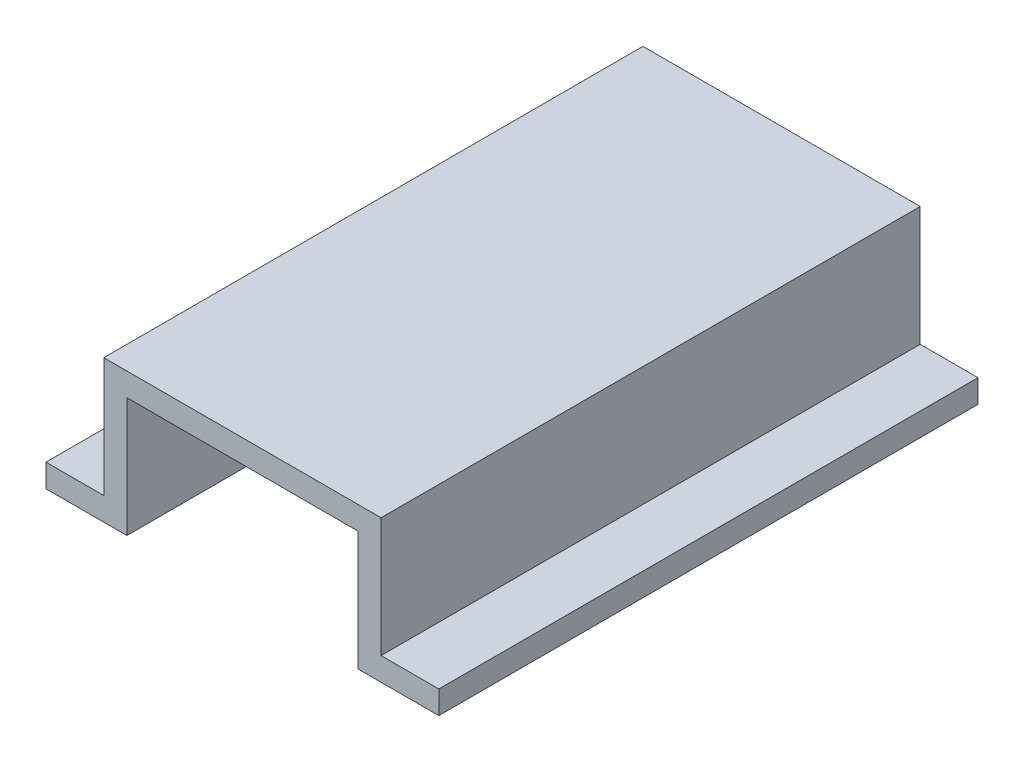
SolidWorks part; units mm, degrees
ref_plane "Front Plane" through (0, 0, 0) normal (0, 0, 1) x (1, 0, 0)
ref_plane "Top Plane" through (0, 0, 0) normal (0, 1, 0) x (1, 0, 0)
ref_plane "Right Plane" through (0, 0, 0) normal (1, 0, 0) x (0, 0, -1)
sketch "Sketch1" plane through (0, 0, 0) normal (0, 0, 1) x (1, 0, 0)
  line L0 (0, 0) -> (15, 0)
  line L1 (15, 0) -> (15, 31)
  line L2 (15, 31) -> (87, 31)
  line L3 (87, 31) -> (87, 0)
  line L4 (87, 0) -> (102, 0)
  line L5 (102, 0) -> (102, -6)
  line L6 (102, -6) -> (81, -6)
  line L7 (81, -6) -> (81, 25)
  line L8 (81, 25) -> (21, 25)
  line L9 (21, 25) -> (21, -6)
  line L10 (21, -6) -> (0, -6)
  line L11 (0, -6) -> (0, 0)
  dimension "D1" = 6
  dimension "D2" = 6
  dimension "D3" = 60
  dimension "D4" = 6
  dimension "D5" = 6
  dimension "D6" = 6
  dimension "D7" = 37
  dimension "D8" = 15
extrude "Boss-Extrude1" add sketch "Sketch1" along normal blind 140
